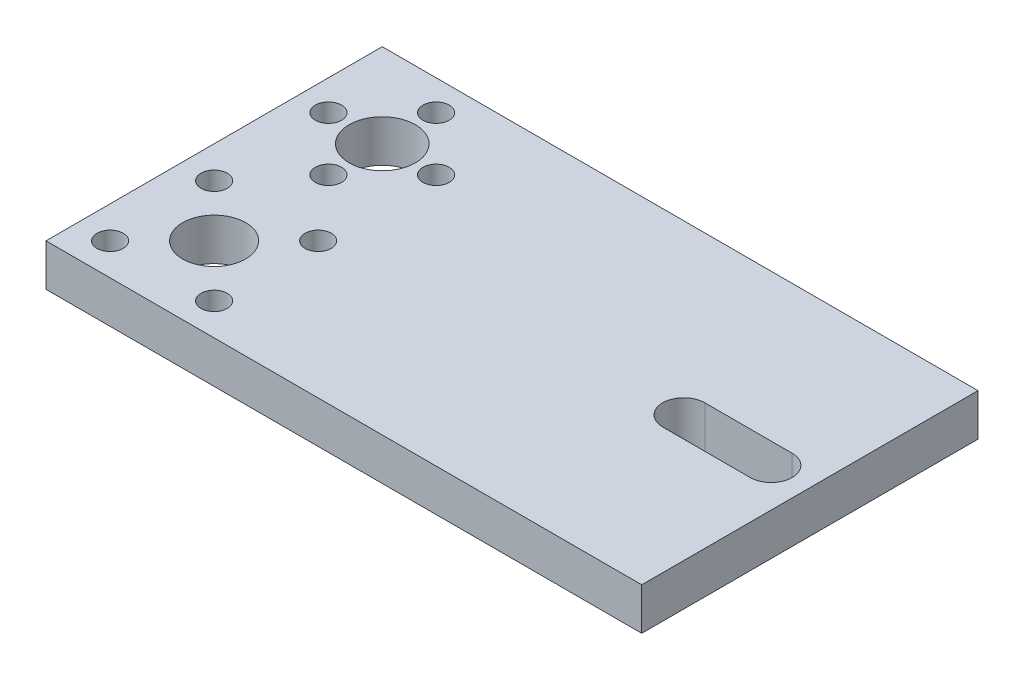
SolidWorks part; units mm, degrees
material "AISI 1020"
ref_plane "Front Plane" through (0, 0, 0) normal (0, 0, 1) x (1, 0, 0)
ref_plane "Top Plane" through (0, 0, 0) normal (0, 1, 0) x (1, 0, 0)
ref_plane "Right Plane" through (0, 0, 0) normal (1, 0, 0) x (0, 0, -1)
sketch "Sketch1" plane through (0, 0, 0) normal (0, 1, 0) x (1, 0, 0)
  line L0 (40, -12.7) -> (25.0632, -12.7) construction
  line L1 (-50, -38.1) -> (40, -38.1)
  line L2 (-50, -38.1) -> (-50, 12.7)
  line L4 (40, -38.1) -> (40, 12.7)
  line L5 (-50, 0) -> (40, 0) construction
  line L6 (20.945, -9.525) -> (34.155, -9.525)
  line L7 (20.945, -15.875) -> (34.155, -15.875)
  line L10 (-43.8422, -18.8578) -> (-30.7578, -31.9422) construction
  line L11 (-50, 12.7) -> (40, 12.7)
  line L16 (-30.7578, -31.9422) -> (-43.8422, -18.8578) construction
  line L17 (-30.7578, -18.8578) -> (-43.8422, -31.9422) construction
  line L18 (-43.8422, -31.9422) -> (-30.7578, -18.8578) construction
  circle A0 centre (-37.3, 0) radius 5
  circle A3 centre (-37.3, -8.13) radius 1.9844
  circle A9 centre (-45.43, 0) radius 1.9844
  circle A10 centre (-37.3, 8.13) radius 1.9844
  circle A11 centre (-29.17, 0) radius 1.9844
  circle A13 centre (-37.3, -25.4) radius 4.7625
  arc A17 (34.155, -15.875) -> (34.155, -9.525) centre (34.155, -12.7) ccw
  arc A18 (20.945, -9.525) -> (20.945, -15.875) centre (20.945, -12.7) ccw
  circle A19 centre (-37.3, -25.4) radius 11.1125 construction
  circle A20 centre (-45.1577, -17.5423) radius 1.9844
  circle A21 centre (-29.4423, -17.5423) radius 1.9844
  circle A22 centre (-29.4423, -33.2577) radius 1.9844
  circle A23 centre (-45.1577, -33.2577) radius 1.9844
  point P0 (0, 0)
  dimension "D3" = 10
  dimension "D5" = 6.35
  dimension "D6" = 3.9688
  dimension "D9" = 50.8
  dimension "D10" = 12.7
  dimension "D12" = 13.21
  dimension "D13" = 5.845
  dimension "D11" = 6.35
  dimension "D15" = 3.9688
  dimension "D17" = 22.225
  dimension "D18" = 9.525
  dimension "D2" = 90
  dimension "D4" = 12.7
  dimension "D7" = 8.13
  dimension "D14" = 38.1
  dimension "D19" = 25.4
  dimension "D8" = 4
  dimension "D16" = 4
extrude "Boss-Extrude1" add sketch "Sketch1" along normal blind 6.35
